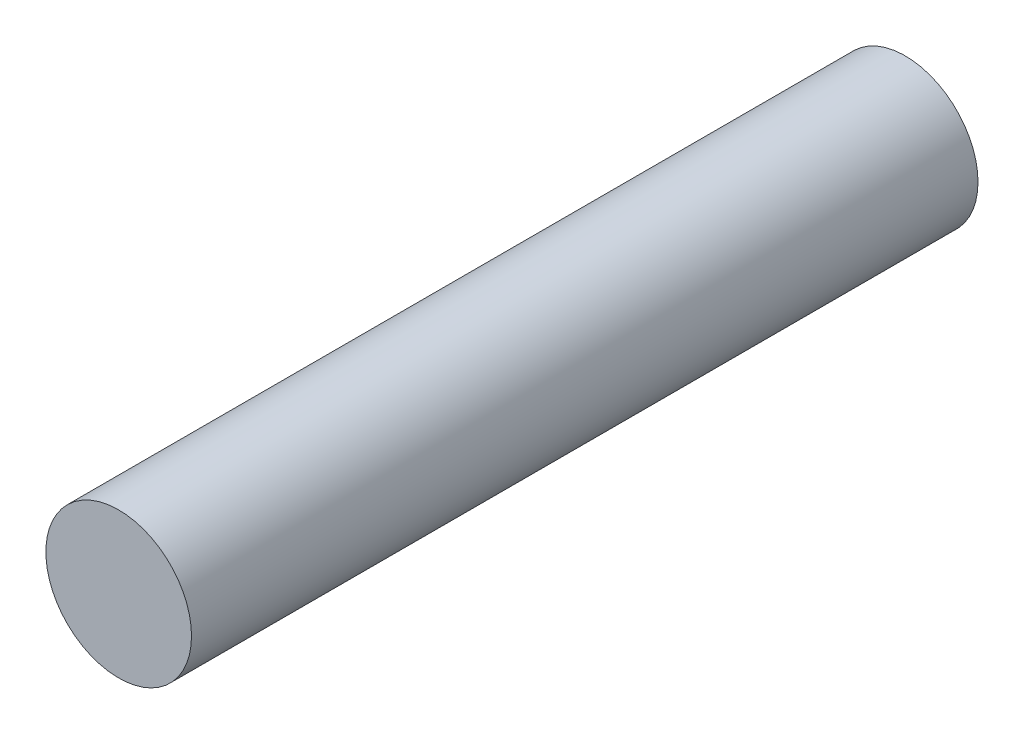
SolidWorks part; units mm, degrees
ref_plane "Front Plane" through (0, 0, 0) normal (0, 0, 1) x (1, 0, 0)
ref_plane "Top Plane" through (0, 0, 0) normal (0, 1, 0) x (1, 0, 0)
ref_plane "Right Plane" through (0, 0, 0) normal (1, 0, 0) x (0, 0, -1)
sketch "Sketch1" plane through (0, 0, 0) normal (0, 0, 1) x (1, 0, 0)
  circle A0 centre (0, 0) radius 12.5
  dimension "D1" = 25
extrude "Boss-Extrude1" add sketch "Sketch1" along normal blind 135
